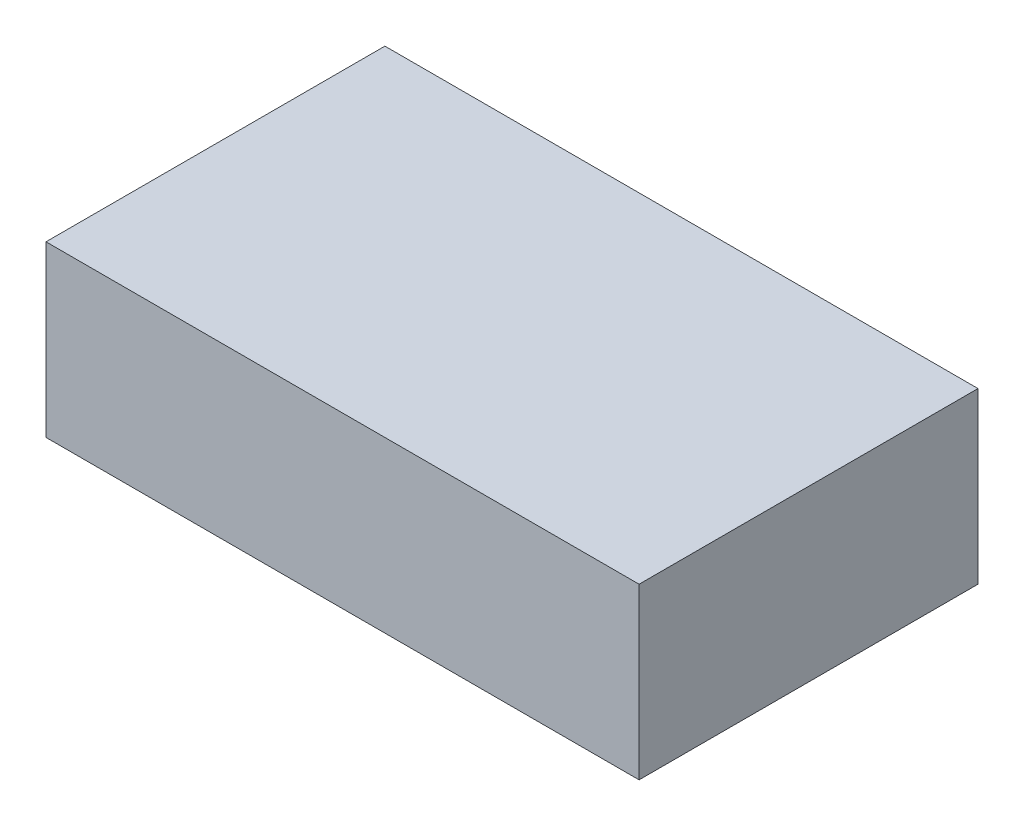
SolidWorks part; units mm, degrees
ref_plane "Front Plane" through (0, 0, 0) normal (0, 0, 1) x (1, 0, 0)
ref_plane "Top Plane" through (0, 0, 0) normal (0, 1, 0) x (1, 0, 0)
ref_plane "Right Plane" through (0, 0, 0) normal (1, 0, 0) x (0, 0, -1)
sketch "Sketch1" plane through (0, 0, 0) normal (0, 1, 0) x (1, 0, 0)
  line L1 (-350, 200) -> (350, 200)
  line L2 (-350, 200) -> (-350, -200)
  line L3 (-350, -200) -> (350, -200)
  line L4 (350, 200) -> (350, -200)
  line L5 (-350, 200) -> (350, -200) construction
  line L6 (-350, -200) -> (350, 200) construction
  point P0 (0, 0)
  dimension "D1" = 700
  dimension "D2" = 400
extrude "Boss-Extrude1" add sketch "Sketch1" along normal blind 200
